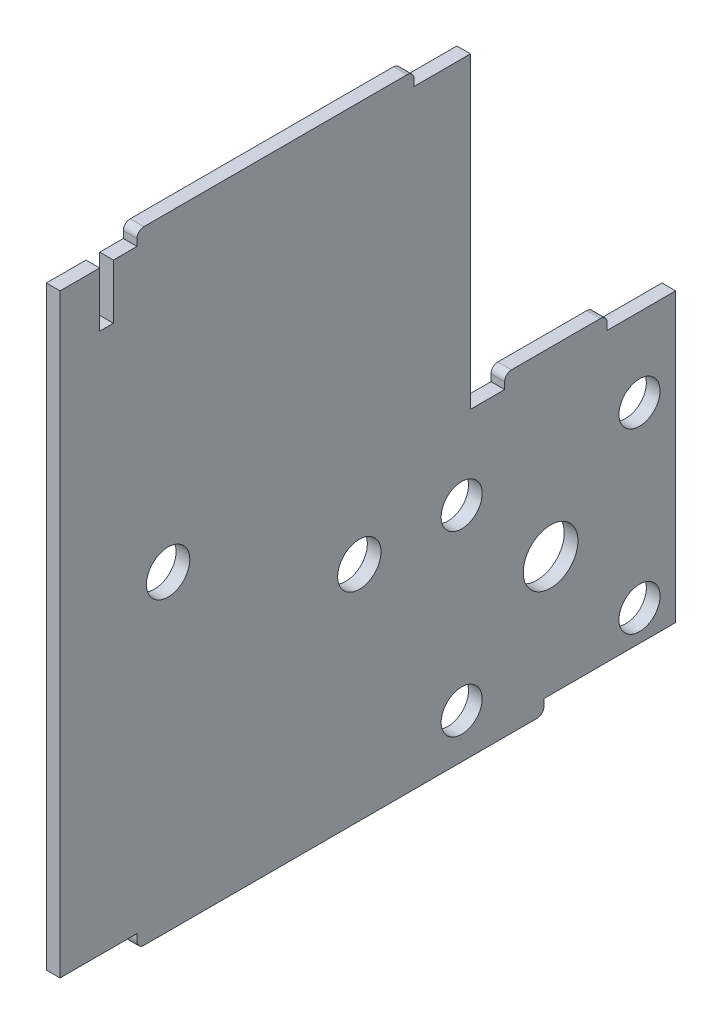
SolidWorks part; units mm, degrees
ref_plane "Front Plane" through (0, 0, 0) normal (0, 0, 1) x (1, 0, 0)
ref_plane "Top Plane" through (0, 0, 0) normal (0, 1, 0) x (1, 0, 0)
ref_plane "Right Plane" through (0, 0, 0) normal (1, 0, 0) x (0, 0, -1)
sketch "Sketch1" plane through (0, 0, 0) normal (1, 0, 0) x (0, 0, -1)
  line L0 (22.0988, -49.5112) -> (22.0988, -7.5112)
  line L1 (-7.9012, -7.5112) -> (-7.9012, 37.4888)
  line L2 (22.0988, -7.5112) -> (2.8483, -7.5112) construction
  line L3 (11.0988, -5.5112) -> (-1.9012, -5.5112)
  line L4 (-7.9012, -49.5112) -> (-7.9012, 37.4888) construction
  line L5 (-56.6507, -49.5112) -> (-56.6507, -50.5112)
  line L6 (-60.1012, 37.4888) -> (-56.6507, 37.4888)
  line L7 (22.0988, -49.5112) -> (2.8483, -49.5112)
  line L8 (-67.9012, -49.5112) -> (-56.6507, -49.5112)
  line L9 (22.0988, -7.5112) -> (12.0988, -7.5112)
  line L10 (-2.9012, -7.5112) -> (-2.9012, -6.5112)
  line L11 (-17.1517, 39.4888) -> (-55.6507, 39.4888)
  line L12 (2.8483, -49.5112) -> (2.8483, -50.5112)
  line L13 (12.0988, -7.5112) -> (12.0988, -6.5112)
  line L14 (-2.9012, -7.5112) -> (-7.9012, -7.5112)
  line L15 (-16.1517, 37.4888) -> (-7.9012, 37.4888)
  line L16 (-56.6507, 37.4888) -> (-56.6507, 38.4888)
  line L17 (22.0988, -5.5112) -> (-7.9012, -5.5112) construction
  line L18 (-55.6507, -51.5112) -> (1.8483, -51.5112)
  line L20 (-16.1517, 37.4888) -> (-16.1517, 38.4888)
  line L21 (22.0988, -7.5112) -> (-7.9012, -7.5112) construction
  line L22 (22.0988, -49.5112) -> (22.0988, 37.4888) construction
  line L23 (-67.9012, -49.5112) -> (-67.9012, 37.4888)
  line L26 (-60.1012, 29.4888) -> (-62.1012, 29.4888)
  line L29 (-60.1012, 29.4888) -> (-60.1012, 37.4888)
  line L30 (-62.1012, 37.4888) -> (-67.9012, 37.4888)
  line L32 (-62.1012, 29.4888) -> (-62.1012, 37.4888)
  arc A0 (-55.6507, -51.5112) -> (-56.6507, -50.5112) centre (-55.6507, -50.5112) cw
  arc A1 (12.0988, -6.5112) -> (11.0988, -5.5112) centre (11.0988, -6.5112) ccw
  circle A2 centre (3.8133, -32.0112) radius 4
  arc A3 (-2.9012, -6.5112) -> (-1.9012, -5.5112) centre (-1.9012, -6.5112) cw
  arc A4 (1.8483, -51.5112) -> (2.8483, -50.5112) centre (1.8483, -50.5112) ccw
  arc A5 (-16.1517, 38.4888) -> (-17.1517, 39.4888) centre (-17.1517, 38.4888) ccw
  arc A6 (-56.6507, 38.4888) -> (-55.6507, 39.4888) centre (-55.6507, 38.4888) cw
  circle A7 centre (-9.1867, -19.0112) radius 3
  circle A8 centre (16.8133, -19.0112) radius 3
  circle A9 centre (16.8133, -45.0112) radius 3
  circle A10 centre (-9.1867, -45.0112) radius 3
  circle A12 centre (-52.1012, -6.0112) radius 3.17
  circle A19 centre (-24.144, -19.0112) radius 3.17
extrude "Boss-Extrude1" add sketch "Sketch1" along normal blind 2
